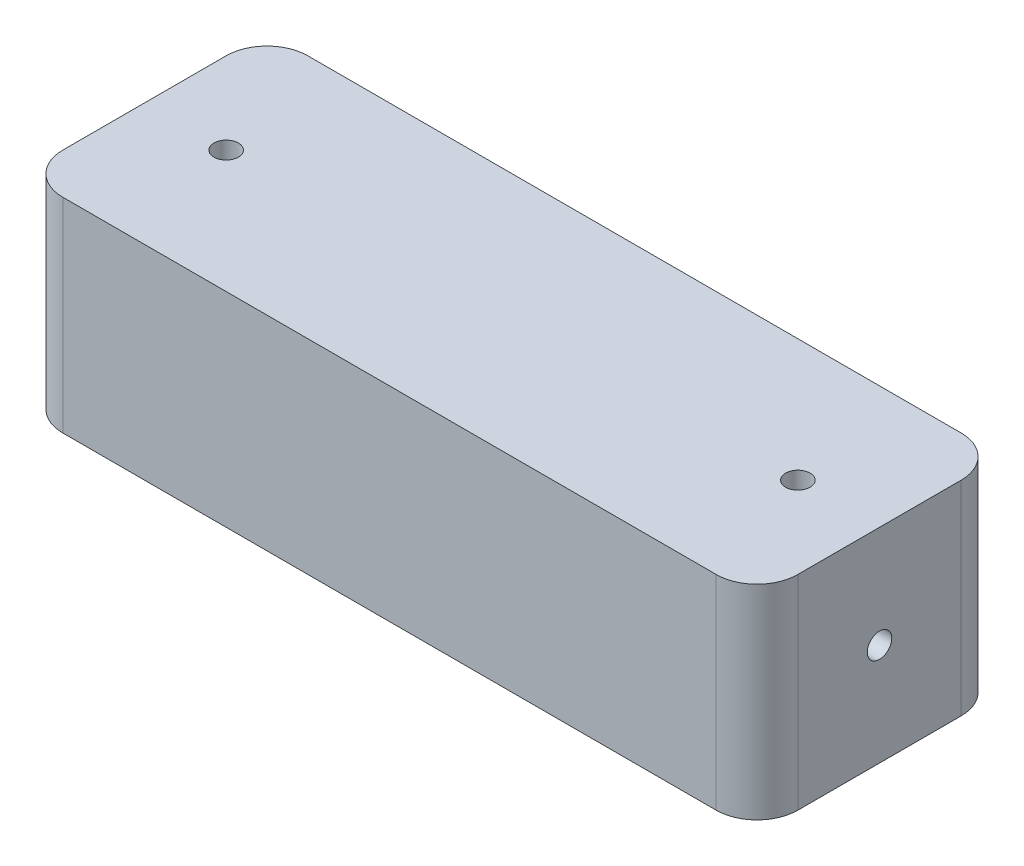
SolidWorks part; units mm, degrees
material "ABS"
ref_plane "Front Plane" through (0, 0, 0) normal (0, 0, 1) x (1, 0, 0)
ref_plane "Top Plane" through (0, 0, 0) normal (0, 1, 0) x (1, 0, 0)
ref_plane "Right Plane" through (0, 0, 0) normal (1, 0, 0) x (0, 0, -1)
sketch "Sketch1" plane through (0, 0, 0) normal (0, 1, 0) x (1, 0, 0)
  line L0 (90, 60) -> (90, 0) construction
  line L1 (0, 0) -> (180, 0)
  line L2 (0, 0) -> (0, 60)
  line L3 (0, 60) -> (180, 60)
  line L4 (180, 0) -> (180, 60)
  circle A0 centre (20, 30) radius 3
  circle A1 centre (160, 30) radius 3
  point P9 (0, 30)
  dimension "D3" = 6
  dimension "D4" = 20
  dimension "D1" = 60
  dimension "D2" = 180
extrude "Boss-Extrude1" add sketch "Sketch1" along normal blind 50
sketch "Sketch2" plane through (180, 0, 0) normal (1, 0, 0) x (0, 0, -1)
  line L0 (30, 50) -> (30, 0) construction
  line L1 (0, 50) -> (60, 50) construction
  line L2 (0, 0) -> (60, 0) construction
  line L3 (60, 25) -> (0, 25) construction
  line L4 (60, 50) -> (60, 0) construction
  line L5 (0, 50) -> (0, 0) construction
  circle A0 centre (30, 25) radius 3
  dimension "D1" = 6
extrude "Cut-Extrude1" cut sketch "Sketch2" against normal blind 10
fillet "Fillet1" radius 10 4 edges at (180, 25, -60) (180, 25, 0) (0, 25, 0) (0, 25, -60)
